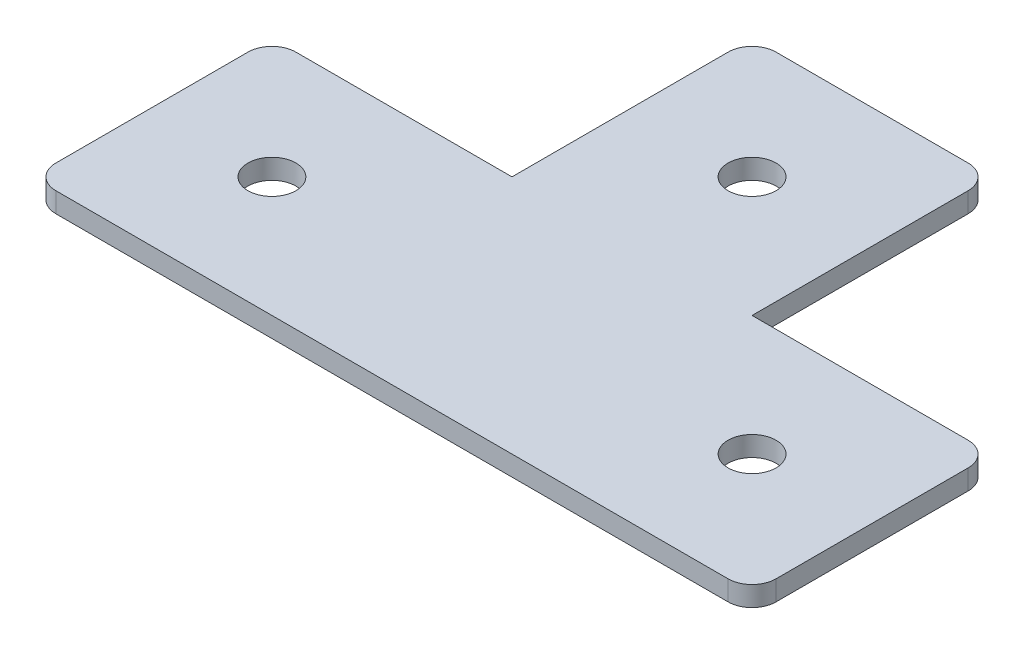
SolidWorks part; units mm, degrees
ref_plane "Front Plane" through (0, 0, 0) normal (0, 0, 1) x (1, 0, 0)
ref_plane "Top Plane" through (0, 0, 0) normal (0, 1, 0) x (1, 0, 0)
ref_plane "Right Plane" through (0, 0, 0) normal (1, 0, 0) x (0, 0, -1)
sketch "Sketch1" plane through (0, 0, 0) normal (0, 1, 0) x (1, 0, 0)
  line L1 (-12.4699, 24.8494) -> (17.5301, 24.8494)
  line L2 (-12.4699, 24.8494) -> (-12.4699, -5.1506)
  line L3 (-12.4699, -35.1506) -> (17.5301, -35.1506)
  line L4 (17.5301, 24.8494) -> (17.5301, -5.1506)
  line L5 (-12.4699, -35.1506) -> (-42.4699, -35.1506)
  line L7 (-12.4699, -5.1506) -> (-42.4699, -5.1506)
  line L8 (-42.4699, -35.1506) -> (-42.4699, -5.1506)
  line L9 (17.5301, -35.1506) -> (47.5301, -35.1506)
  line L11 (17.5301, -5.1506) -> (47.5301, -5.1506)
  line L12 (47.5301, -35.1506) -> (47.5301, -5.1506)
  dimension "D1" = 30
  dimension "D2" = 60
  dimension "D3" = 30
  dimension "D4" = 30
  dimension "D5" = 30
  dimension "D6" = 30
extrude "Boss-Extrude1" add sketch "Sketch1" along normal blind 2.5
fillet "Fillet1" radius 3 1 edges at (-42.4699, 1.25, 5.1506)
fillet "Fillet2" radius 3 1 edges at (-42.4699, 1.25, 35.1506)
fillet "Fillet4" radius 3 1 edges at (17.5301, 1.25, -24.8494)
fillet "Fillet5" radius 3 1 edges at (-12.4699, 1.25, -24.8494)
sketch "Sketch2" plane through (0, 2.5, 0) normal (0, 1, 0) x (1, 0, 0)
  line L0 (-12.4699, 21.8494) -> (-12.4699, -5.1506) construction
  line L1 (-39.4699, -35.1506) -> (47.5301, -35.1506) construction
  line L2 (-42.4699, -8.1506) -> (-42.4699, -32.1506) construction
  line L3 (14.5301, 24.8494) -> (-9.4699, 24.8494) construction
  line L4 (47.5301, -35.1506) -> (47.5301, -5.1506) construction
  line L5 (47.5301, -5.1506) -> (17.5301, -5.1506) construction
  circle A0 centre (2.5301, 9.8494) radius 3
  circle A1 centre (-27.4699, -20.1506) radius 3
  circle A2 centre (32.5301, -20.1506) radius 3
  dimension "D1" = 15
  dimension "D5" = 15
  dimension "D2" = 15
  dimension "D3" = 15
  dimension "D4" = 15
  dimension "D6" = 15
extrude "Cut-Extrude1" cut sketch "Sketch2" against normal blind 3
fillet "Fillet6" radius 3 1 edges at (47.5301, 1.25, 35.1506)
fillet "Fillet7" radius 3 1 edges at (47.5301, 1.25, 5.1506)
